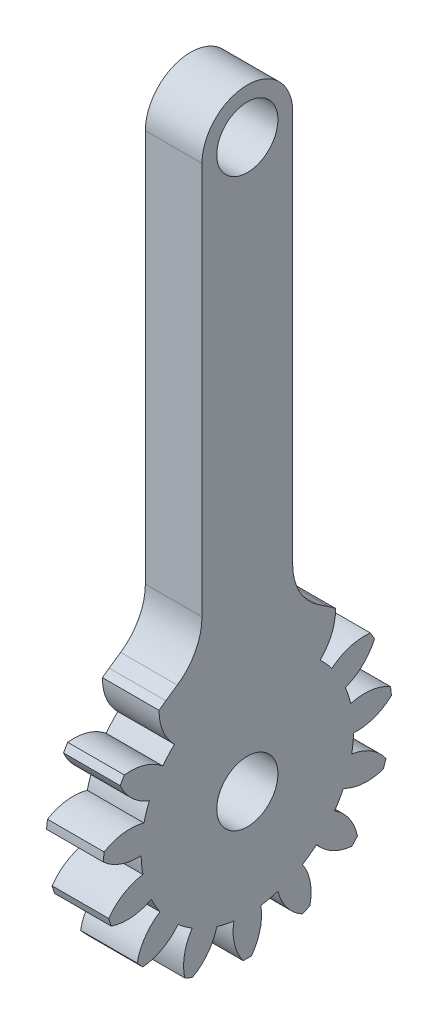
SolidWorks part; units mm, degrees
ref_plane "Plane1" through (0, 0, 0) normal (0, 0, 1) x (1, 0, 0)
ref_plane "Plane2" through (0, 0, 0) normal (0, 1, 0) x (1, 0, 0)
ref_plane "Plane3" through (0, 0, 0) normal (1, 0, 0) x (0, 0, -1)
sketch "HoldingSke" plane through (0, 0, 0) normal (0, 1, 0) x (1, 0, 0)
  line L0 (0, 0) -> (0.644, -0.1725)
  line L1 (-15, 0) -> (100, 0) construction
  line L2 (0, 0) -> (-2.1039, 2.3779)
  line L3 (0, 0) -> (-11.863, 4.5341)
  line L4 (0, 0) -> (8.3417, 2.2352)
  line L5 (0, 0) -> (-46.8476, -17.4728)
  line L6 (0, 0) -> (-4.1448, -2.7965)
  line L7 (-2.1039, 2.3779) -> (8.6589, 51.2074)
  line L8 (-76.2, 54.61) -> (-75.3, 54.61)
  line L9 (-71.009, 38.7566) -> (-53.1078, 45.2721)
  line L10 (-76.2, 71.12) -> (104.1128, 71.12)
  line L11 (0, 0) -> (-5, 0)
  line L12 (-76.2, 101.6) -> (-76.162, 101.6)
  line L13 (24.9733, 27.94) -> (52.9518, 28.4284)
  line L14 (24.9733, 27.94) -> (24.9743, 27.94)
  line L15 (24.9733, 27.94) -> (100.4006, 29.5858)
  line L16 (-63.627, -1.5) -> (-12.827, -1.5)
  circle A0 centre (0, 0) radius 2.7
  circle A1 centre (0, 0) radius 6.249
  circle A2 centre (0, 0) radius 37.5
  circle A3 centre (0, 0) radius 2.7
  dimension "MHD" = 12.498
  dimension "Hub_dia" = 75
  dimension "Bore" = 5.4
  dimension "MBD" = 5.4
  dimension "Num_teeth" = 15
  dimension "Pitch" = 0.6667
  dimension "Overall_len" = 50
  dimension "Show_teeth" = 15
  dimension "Thickness" = 5
  dimension "OAL" = 50.0016
  dimension "T_dim" = 0.9
  dimension "Ap" = 20
  dimension "H" = 19.05
  dimension "Pitch_radius" = 180.3128
  dimension "Width" = 5
  dimension "Backlash" = 0.038
  dimension "Addendum_fac" = 1
  dimension "Dedendum_fac" = 1.25
  dimension "Clearance_fac" = 0.25
  dimension "Dedendum_add" = 0.001
  dimension "Module" = 1.5
sketch "BasProSke" plane through (0, 0, 0) normal (0, 1, 0) x (1, 0, 0)
  line L0 (-10, 0) -> (60, 0) construction
  line L1 (0, 0) -> (0, 12.75)
  line L2 (0, 0) -> (5, 0)
  line L3 (5, 0) -> (5, 12.75)
  line L4 (5, 12.75) -> (0, 12.75)
  dimension "Thickness" = 5
  dimension "Diameter" = 25.5
revolve "Base-Revolve" add sketch "BasProSke" angle 360 about L0
sketch "TooCutSke" plane through (0, 0, 0) normal (1, 0, 0) x (0, 0, -1)
  line L1 (0, 0) -> (0, 107) construction
  line L2 (0, 0) -> (-1.2424, 11.1812) construction
  line L3 (0, 0) -> (-4.6552, 21.901) construction
  line L4 (-1.2424, 11.1812) -> (-2.3276, 10.9505) construction
  arc A0 (0.7696, 9.3424) -> (-0.7696, 9.3424) centre (0, 0) ccw
  arc A1 (2.3153, 12.5638) -> (-2.3153, 12.5638) centre (0, 0) ccw
  circle A2 centre (0, 0) radius 11.25 construction
  circle A3 centre (0, 0) radius 10.5715 construction
  arc A4 (-0.7696, 9.3424) -> (-2.3153, 12.5638) centre (-5.2662, 9.1665) ccw
  arc A5 (2.3153, 12.5638) -> (0.7696, 9.3424) centre (5.2662, 9.1665) ccw
  dimension "Root_dia" = 18.748
  dimension "Overcut_dia" = 25.5508
  dimension "Pitch_dia" = 22.5
  dimension "Base_dia" = 21.1431
  dimension "Flank_rad" = 4.5
  dimension "Half_ang" = 12
  dimension "Half_CT" = 1.1094
extrude "ToothCut" cut sketch "TooCutSke" along normal through all
fillet "Breaks" [suppressed] radius 0.03
fillet "RootFillets" [suppressed] radius 0.376
pattern_circular "TeethCuts" count 15 every 24 about axis through (-10, 0, 0) along (1, 0, 0) of "ToothCut", "RootFillets", "Breaks"
sketch "HubNeaOneSke" plane through (0, 0, 0) normal (-1, 0, 0) x (0, 0, 1)
  circle A0 centre (0, 0) radius 6.249
  dimension "Diameter" = 12.498
extrude "HubNearOne" [suppressed] add sketch "HubNeaOneSke" along normal blind 45.0016
sketch "HubNeaBotSke" plane through (0, 0, 0) normal (-1, 0, 0) x (0, 0, 1)
  circle A0 centre (0, 0) radius 6.249
  dimension "Diameter" = 12.498
extrude "HubNearBoth" [suppressed] add sketch "HubNeaBotSke" along normal blind 22.5008
ref_plane "FarPln" through (5, 0, 0) normal (1, 0, 0) x (0, 0, -1)
sketch "HubFarSke" plane through (5, 0, 0) normal (1, 0, 0) x (0, 0, -1)
  circle A0 centre (0, 0) radius 6.249
  dimension "Diameter" = 12.498
extrude "HubFar" [suppressed] add sketch "HubFarSke" along normal blind 22.5008
sketch "BorSke" plane through (0, 0, 0) normal (1, 0, 0) x (0, 0, -1)
  circle A0 centre (0, 0) radius 2.7
  dimension "Diameter" = 5.4
extrude "Bore" cut sketch "BorSke" along normal mid plane 100.0031
sketch "KeySke" plane through (0, 0, 0) normal (1, 0, 0) x (0, 0, -1)
  line L0 (-1, 0) -> (-1, 3.6)
  line L1 (-1, 3.6) -> (1, 3.6)
  line L2 (1, 3.6) -> (1, 0)
  line L3 (0, 0) -> (0, 34) construction
  line L4 (-1, 0) -> (1, 0)
  dimension "Offset" = 3.6
  dimension "Width" = 2
extrude "Keyway" [suppressed] cut sketch "KeySke" along normal mid plane 100.0031
pattern_circular "Keyway2" [suppressed] count 2 every 90 about axis through (-10, 0, 0) along (1, 0, 0)
sketch "Sketch1" plane through (0, 0, 0) normal (-1, 0, 0) x (0, 0, 1)
  line L12 (4, 12.7095) -> (4, 50)
  line L13 (4, 50) -> (-4, 50) construction
  line L14 (-4, 50) -> (-4, 12.7095)
  line L16 (-7.1943, 10.5264) -> (-4.503, 8.2216)
  line L17 (-4.503, 8.2216) -> (4.503, 8.2216)
  line L18 (4.503, 8.2216) -> (7.1943, 10.5264)
  line L19 (7.1943, 10.5264) -> (4, 12.7095)
  line L20 (-7.1943, 10.5264) -> (-4, 12.7095)
  arc A0 (-4, 50) -> (4, 50) centre (0, 50) cw
  arc A1 (-7.1943, 10.5264) -> (-7.788, 10.095) centre (0, 0) ccw construction
  arc A5 (7.788, 10.095) -> (7.1943, 10.5264) centre (0, 0) ccw construction
  circle A6 centre (0, 50) radius 2.7
  dimension "D1" = 8
  dimension "D2" = 50
  dimension "D3" = 5.4
extrude "Boss-Extrude1" add sketch "Sketch1" against normal up to surface (5 mm away) up to face at (5, 0, 2.7)
fillet "Fillet1" radius 5 2 edges at (2.5, 12.7095, -4) (2.5, 12.7095, 4)
equation "' \"Module@HoldingSke\" = 6.35"
equation "' \"Num_teeth@HoldingSke\" = 12"
equation "' \"Ap@HoldingSke\" =  20"
equation "' \"Ap@HoldingSke\" = 20"
equation "' \"Width@HoldingSke\" = 0.5 * 25.4"
equation "' \"Hub_dia@HoldingSke\"= 1 * 25.4"
equation "' \"Hub_dia@HoldingSke\" = 1 * 25.4"
equation "' \"Overall_len@HoldingSke\" = 1.0 * 25.4"
equation "' \"Bore@HoldingSke\" = 0.75 * 25.4"
equation "' \"T_dim@HoldingSke\" = 0.1 * 25.4"
equation "' \"Width@KeySke\" = 0.25 * 25.4"
equation "' \"Show_teeth@HoldingSke\" = 13"
equation "' \"Backlash@HoldingSke\" = 0.009 * 25.4"
equation "' \"Addendum_fac@HoldingSke\" = 1.0"
equation "' \"Dedendum_fac@HoldingSke\" = 1.25"
equation "' \"Dedendum_add@HoldingSke\" = 0.00005 * 25.4"
equation "' \"Clearance_fac@HoldingSke\" = 0.25"
equation "\"Pitch@HoldingSke\" = 1 / \"Module@HoldingSke\""
equation "\"Overcut_dia@TooCutSke\" = (\"Num_teeth@HoldingSke\" + 2 * \"Addendum_fac@HoldingSke\") / \"Pitch@HoldingSke\" + 0.002 * 25.4"
equation "\"Pitch_dia@TooCutSke\" = \"Num_teeth@HoldingSke\" / \"Pitch@HoldingSke\""
equation "\"Base_dia@TooCutSke\" = \"Num_teeth@HoldingSke\" / \"Pitch@HoldingSke\" * cos((\"Ap@HoldingSke\"  * 3.14159265 / 180))"
equation "\"Root_dia@TooCutSke\" = (\"Num_teeth@HoldingSke\" + 2) / \"Pitch@HoldingSke\" - 2 * (\"Addendum_fac@HoldingSke\" + \"Dedendum_fac@HoldingSke\") / \"Pitch@HoldingSke\" - \"Dedendum_add@HoldingSke\" * 2"
equation "\"Half_ang@TooCutSke\" = 180 / \"Num_teeth@HoldingSke\""
equation "\"Half_CT@TooCutSke\" = \"Num_teeth@HoldingSke\" / \"Pitch@HoldingSke\" * sin((3.14159265 / 2 / \"Num_teeth@HoldingSke\")) / 2 - 7 * \"Backlash@HoldingSke\" / 4"
equation "\"Flank_rad@TooCutSke\" = \"Num_teeth@HoldingSke\" / \"Pitch@HoldingSke\" / 5"
equation "\"Radius@RootFillets\" = \"Clearance_fac@HoldingSke\" / \"Pitch@HoldingSke\" + \"Dedendum_add@HoldingSke\""
equation "\"Break_rad@Breaks\" = 0.02 / \"Pitch@HoldingSke\""
equation "\"Thickness@HoldingSke\" = \"Width@HoldingSke\""
equation "\"OAL@HoldingSke\" = \"Thickness@HoldingSke\""
equation "\"MHD@HoldingSke\" = (\"Num_teeth@HoldingSke\" + 2) / \"Pitch@HoldingSke\" - 2 * (\"Addendum_fac@HoldingSke\" + \"Dedendum_fac@HoldingSke\")  / \"Pitch@HoldingSke\" - \"Dedendum_add@HoldingSke\" * 2"
equation "\"MBD@HoldingSke\" = (\"Num_teeth@HoldingSke\" + 2) / \"Pitch@HoldingSke\" - 2 * (\"Addendum_fac@HoldingSke\" + \"Dedendum_fac@HoldingSke\")  / \"Pitch@HoldingSke\" - \"Dedendum_add@HoldingSke\" * 2 - 0.002 * 25.4"
equation "\"MHD@HoldingSke\" = ((sgn( \"MHD@HoldingSke\" - \"Hub_dia@HoldingSke\" )-1)*( \"MHD@HoldingSke\" - \"Hub_dia@HoldingSke\" ))/-2+ \"Hub_dia@HoldingSke\""
equation "\"MBD@HoldingSke\"=\"Bore@HoldingSke\""
equation "\"OAL@HoldingSke\" = ((sgn( \"OAL@HoldingSke\" - \"Overall_len@HoldingSke\" )+1)*( \"OAL@HoldingSke\" - \"Overall_len@HoldingSke\" ))/2 + \"Overall_len@HoldingSke\" + 0.000002 * 25.4"
equation "\"Num_teeth@TeethCuts\" = int( \"Show_teeth@HoldingSke\" ) + 1"
equation "\"Num_teeth@TeethCuts\" = ((sgn( \"Num_teeth@TeethCuts\" - \"Num_teeth@HoldingSke\" )-1)*( \"Num_teeth@TeethCuts\" - \"Num_teeth@HoldingSke\" ))/-2+ \"Num_teeth@HoldingSke\""
equation "\"Num_teeth@TeethCuts\" = ((sgn( \"Num_teeth@TeethCuts\" - 2.0)+1)*( \"Num_teeth@TeethCuts\" - 2.0))/2 +2.0"
equation "\"Angle@TeethCuts\" = 360.0 / \"Num_teeth@HoldingSke\""
equation "\"Diameter@BasProSke\" = (\"Num_teeth@HoldingSke\" + 2 * \"Addendum_fac@HoldingSke\") / \"Pitch@HoldingSke\""
equation "\"Thickness@BasProSke\"  = \"Thickness@HoldingSke\""
equation "' \"Fillet_rad@BasProSke\" =  \"Thickness@HoldingSke\" * 0.05"
equation "' \"Fillet_rad@BasProSke\" = \"Thickness@HoldingSke\" * 0.05"
equation "\"MHD@HoldingSke\" = ((sgn( \"MHD@HoldingSke\" - \"Root_dia@TooCutSke\" )-1)*( \"MHD@HoldingSke\" - \"Root_dia@TooCutSke\" ))/-2+ \"Root_dia@TooCutSke\""
equation "\"Diameter@HubNeaOneSke\" = \"MHD@HoldingSke\""
equation "\"Length@HubNearOne\" = \"OAL@HoldingSke\" - \"Thickness@BasProSke\""
equation "\"Diameter@HubNeaBotSke\" = \"MHD@HoldingSke\""
equation "\"Length@HubNearBoth\" = ( \"OAL@HoldingSke\" - \"Thickness@BasProSke\" ) / 2.0"
equation "\"Thickness@FarPln\" = \"Thickness@BasProSke\""
equation "\"Diameter@HubFarSke\" = \"MHD@HoldingSke\""
equation "\"Length@HubFar\" = ( \"OAL@HoldingSke\" - \"Thickness@BasProSke\" ) / 2.0"
equation "\"Diameter@BorSke\" = \"MBD@HoldingSke\""
equation "\"D1@Bore\" = \"OAL@HoldingSke\" * 2.0"
equation "\"D1@Keyway\" = \"OAL@HoldingSke\" * 2.0"
equation "\"Offset@KeySke\" = \"T_dim@HoldingSke\" + \"MBD@HoldingSke\" / 2.0"
